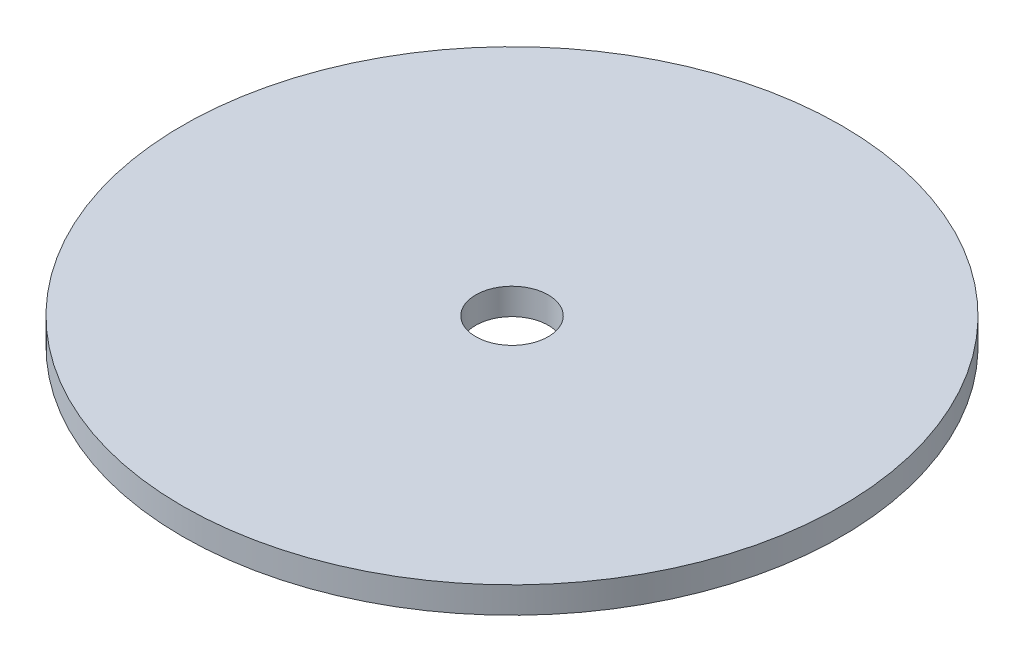
SolidWorks part; units mm, degrees
ref_plane "Front Plane" through (0, 0, 0) normal (0, 0, 1) x (1, 0, 0)
ref_plane "Top Plane" through (0, 0, 0) normal (0, 1, 0) x (1, 0, 0)
ref_plane "Right Plane" through (0, 0, 0) normal (1, 0, 0) x (0, 0, -1)
sketch "Sketch1" plane through (0, 0, 0) normal (0, 1, 0) x (1, 0, 0)
  circle A0 centre (0, 0) radius 4.125
  circle A1 centre (0, 0) radius 37.5
  dimension "D1" = 8.25
  dimension "D2" = 75
extrude "Boss-Extrude1" add sketch "Sketch1" along normal blind 3
